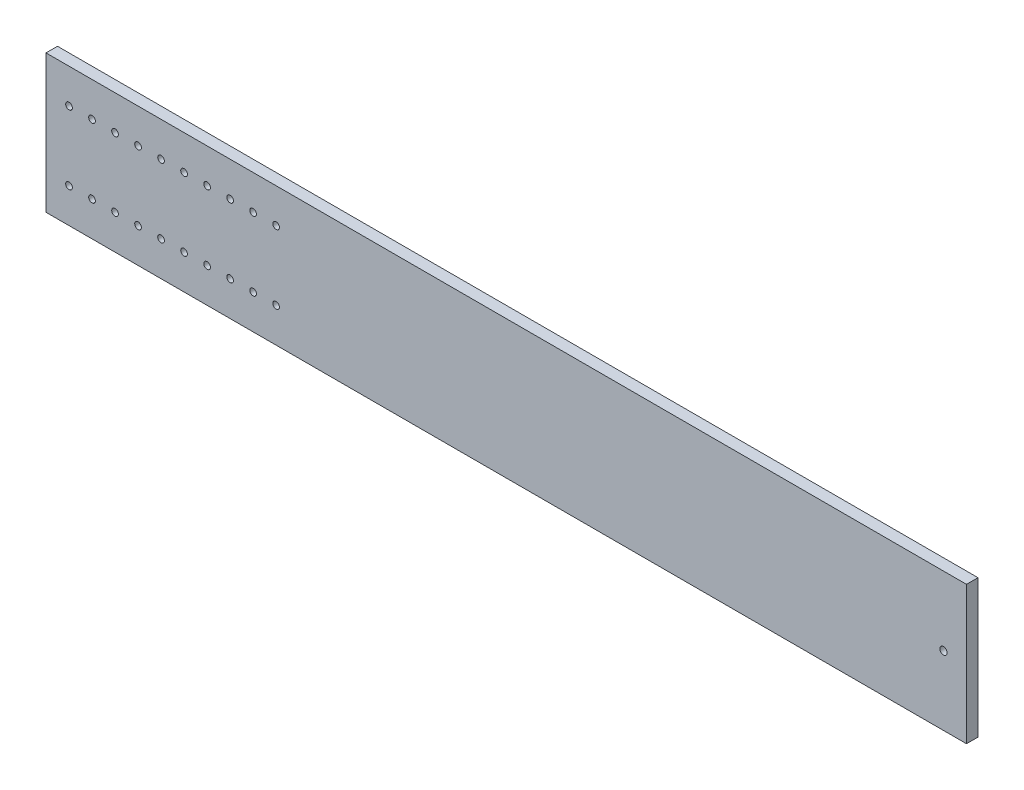
SolidWorks part; units mm, degrees
ref_plane "Front" through (0, 0, 0) normal (0, 0, 1) x (1, 0, 0)
ref_plane "Top" through (0, 0, 0) normal (0, 1, 0) x (1, 0, 0)
ref_plane "Right" through (0, 0, 0) normal (1, 0, 0) x (0, 0, -1)
sketch "Sketch1" plane through (0, 0, 0) normal (0, 0, 1) x (1, 0, 0)
  line L1 (0, 0) -> (508, 0)
  line L2 (0, 0) -> (0, 76.2)
  line L3 (0, 76.2) -> (508, 76.2)
  line L4 (508, 0) -> (508, 76.2)
  dimension "D1" = 508
  dimension "D2" = 76.2
extrude "basic_plank" add sketch "Sketch1" along normal blind 6.35
sketch "Sketch2" plane through (0, 0, 6.35) normal (0, 0, 1) x (1, 0, 0)
  line L0 (508, 76.2) -> (0, 76.2) construction
  line L3 (0, 76.2) -> (0, 0) construction
  circle A0 centre (12.7, 57.15) radius 1.8415
  circle A1 centre (25.4, 57.15) radius 1.8415
  circle A2 centre (38.1, 57.15) radius 1.8415
  circle A3 centre (50.8, 57.15) radius 1.8415
  circle A4 centre (63.5, 57.15) radius 1.8415
  circle A5 centre (76.2, 57.15) radius 1.8415
  circle A6 centre (88.9, 57.15) radius 1.8415
  circle A7 centre (101.6, 57.15) radius 1.8415
  circle A8 centre (114.3, 57.15) radius 1.8415
  circle A9 centre (127, 57.15) radius 1.8415
  circle A10 centre (12.7, 19.05) radius 1.8415
  circle A11 centre (25.4, 19.05) radius 1.8415
  circle A12 centre (38.1, 19.05) radius 1.8415
  circle A13 centre (50.8, 19.05) radius 1.8415
  circle A14 centre (63.5, 19.05) radius 1.8415
  circle A15 centre (76.2, 19.05) radius 1.8415
  circle A16 centre (88.9, 19.05) radius 1.8415
  circle A17 centre (101.6, 19.05) radius 1.8415
  circle A18 centre (114.3, 19.05) radius 1.8415
  circle A19 centre (127, 19.05) radius 1.8415
  dimension "D1" = 3.683
  dimension "D2" = 19.05
  dimension "D3" = 12.7
  dimension "D4" = 10
  dimension "D5" = 2
extrude "placement holes" cut sketch "Sketch2" against normal through all
sketch "Sketch3" plane through (0, 0, 6.35) normal (0, 0, 1) x (1, 0, 0)
  line L0 (508, 0) -> (508, 76.2) construction
  line L1 (508, 76.2) -> (0, 76.2) construction
  circle A0 centre (495.3, 38.1) radius 2.0066
  dimension "D1" = 4.0132
  dimension "D3" = 38.1
  dimension "D2" = 12.7
extrude "wheel_hole" cut sketch "Sketch3" against normal through all
